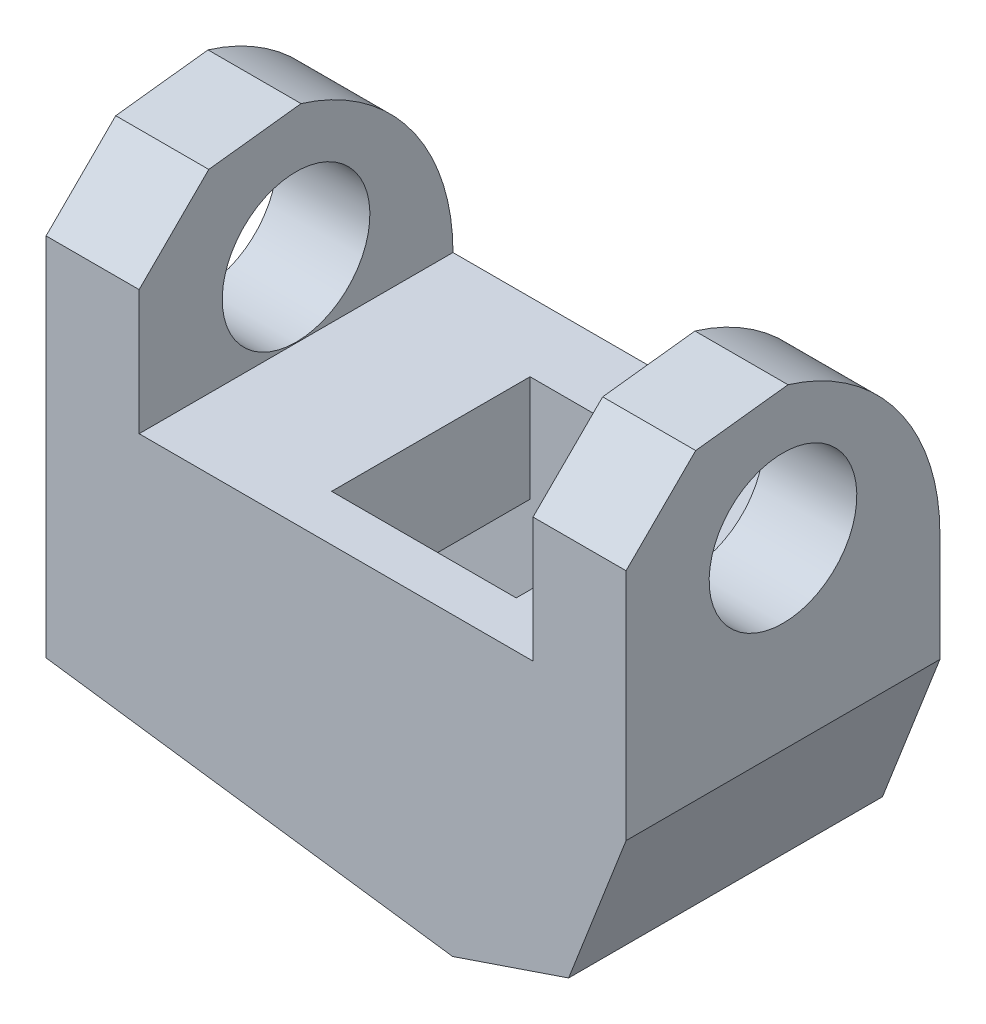
SolidWorks part; units mm, degrees
ref_plane "Plan de face" through (0, 0, 0) normal (0, 0, 1) x (1, 0, 0)
ref_plane "Plan de dessus" through (0, 0, 0) normal (0, 1, 0) x (1, 0, 0)
ref_plane "Plan de droite" through (0, 0, 0) normal (1, 0, 0) x (0, 0, -1)
sketch "Sketch1" plane through (0, 0, 0) normal (0, 0, 1) x (1, 0, 0)
  line L0 (0, 0) -> (0, 11.1)
  line L1 (0, 11.1) -> (5.04, 11.1)
  line L2 (5.04, 11.1) -> (5.04, -5.9)
  line L3 (5.04, -5.9) -> (1.929, -13.9)
  line L4 (1.929, -13.9) -> (-4.3586, -16.0344)
  line L5 (-4.3586, -16.0344) -> (-26.3756, -13.037)
  line L7 (-26.3756, -13.037) -> (-26.3756, 11.1)
  line L8 (-26.3756, 11.1) -> (-21.3356, 11.1)
  line L9 (-21.3356, 11.1) -> (-21.3356, 0)
  line L10 (-21.3356, 0) -> (0, 0)
  dimension "D1" = 5.04
  dimension "D2" = 5.04
  dimension "D3" = 17
  dimension "D4" = 158.75
  dimension "D5" = 8
  dimension "D6" = 6.64
  dimension "D7" = 130
  dimension "D8" = 22.22
  dimension "D10" = 21.3356
  dimension "D11" = 21.3356
  dimension "D12" = 11.1
extrude "Boss-Extrude1" add sketch "Sketch1" along normal blind 17
sketch "Sketch2" plane through (0, 0, 0) normal (-1, 0, 0) x (0, 0, 1)
  line L2 (17, 0) -> (17, 6.76)
  line L3 (17, 11.1) -> (17, 0) construction
  line L4 (17, 6.76) -> (13.2281, 10.5122)
  line L6 (13.2281, 10.5122) -> (8.2281, 11.1)
  line L7 (17, 11.1) -> (0, 11.1) construction
  line L9 (0, 11.1) -> (0, 0) construction
  line L10 (17, 6.76) -> (17, 12.8811)
  line L12 (0, 12.8811) -> (0, 0)
  line L13 (0, 12.8811) -> (17, 12.8811)
  arc A0 (8.2281, 11.1) -> (0, 0) centre (11.6012, 0) ccw
  line M6 (0, 11.1) -> (0, 0)
  line M8 (17, 0) -> (17, 11.1)
  line M9 (17, 11.1) -> (0, 11.1)
  dimension "D1" = 6.76
  dimension "D2" = 134.85
  dimension "D3" = 5
  dimension "D4" = 10
extrude "Cut-Extrude1" cut sketch "Sketch2" against normal mid plane 62 contours L13 L12 L10 M9 | A0 M9 M6 | L6 L4 M8 M9
ref_plane "Plane1" through (0, 0, 7) normal (0, 0, 1) x (1, 0, 0)
sketch "Sketch3" plane through (-2.2225, -16.3252, 0) normal (-0.1349, -0.9909, 0) x (-0.9909, 0.1349, 0)
  line L0 (2.1558, -17) -> (2.1558, 0) construction
  line L1 (18.6458, -3.74) -> (6.1758, -3.74)
  line L2 (18.6458, -3.74) -> (18.6458, -14.49)
  line L3 (18.6458, -14.49) -> (6.1758, -14.49)
  line L4 (6.1758, -3.74) -> (6.1758, -14.49)
  line L5 (24.3758, 0) -> (2.1558, 0) construction
  dimension "D1" = 10.75
  dimension "D2" = 12.47
  dimension "D3" = 4.02
  dimension "D4" = 3.74
sketch "Sketch5" plane through (0, 0, 7) normal (0, 0, 1) x (1, 0, 0)
  line L0 (-9.536, -15.3295) -> (-6.5005, -6.6871)
  line L1 (-20.6979, -13.8099) -> (-8.3419, -15.4921) construction
  dimension "D1" = 101.6
  dimension "D2" = 9.16
sweep "Cut-Sweep1" cut profiles "Sketch3" path "Sketch5"
sketch "Sketch6" plane through (0, 0, 0) normal (0, 1, 0) x (1, 0, 0)
  line L0 (5.04, -13.2281) -> (5.04, -8.2281) construction
  line L1 (-3.42, -14.49) -> (-13.42, -14.49)
  line L2 (-3.42, -14.49) -> (-3.42, -3.74)
  line L3 (-3.42, -3.74) -> (-13.42, -3.74)
  line L4 (-13.42, -14.49) -> (-13.42, -3.74)
  line L5 (0, 0) -> (-21.3356, 0) construction
  dimension "D1" = 10.75
  dimension "D2" = 10
  dimension "D3" = 8.46
  dimension "D4" = 3.74
extrude "Cut-Extrude2" cut sketch "Sketch6" against normal up to surface (29.9503 mm away)
ref_plane "Plane2" through (-10.6678, 0, 0) normal (-1, 0, 0) x (0, 0, 1)
sketch "Sketch7" plane through (-10.6678, 0, 0) normal (-1, 0, 0) x (0, 0, 1)
  line L0 (17, -4.5584) -> (0, -4.5584) construction
  line L1 (17, 6.76) -> (17, -13.037) construction
  circle A0 centre (8.5, 4.0416) radius 4
  dimension "D2" = 8
  dimension "D1" = 8.6
  dimension "D3" = 8.5
extrude "Cut-Extrude3" cut sketch "Sketch7" against normal mid plane 62
